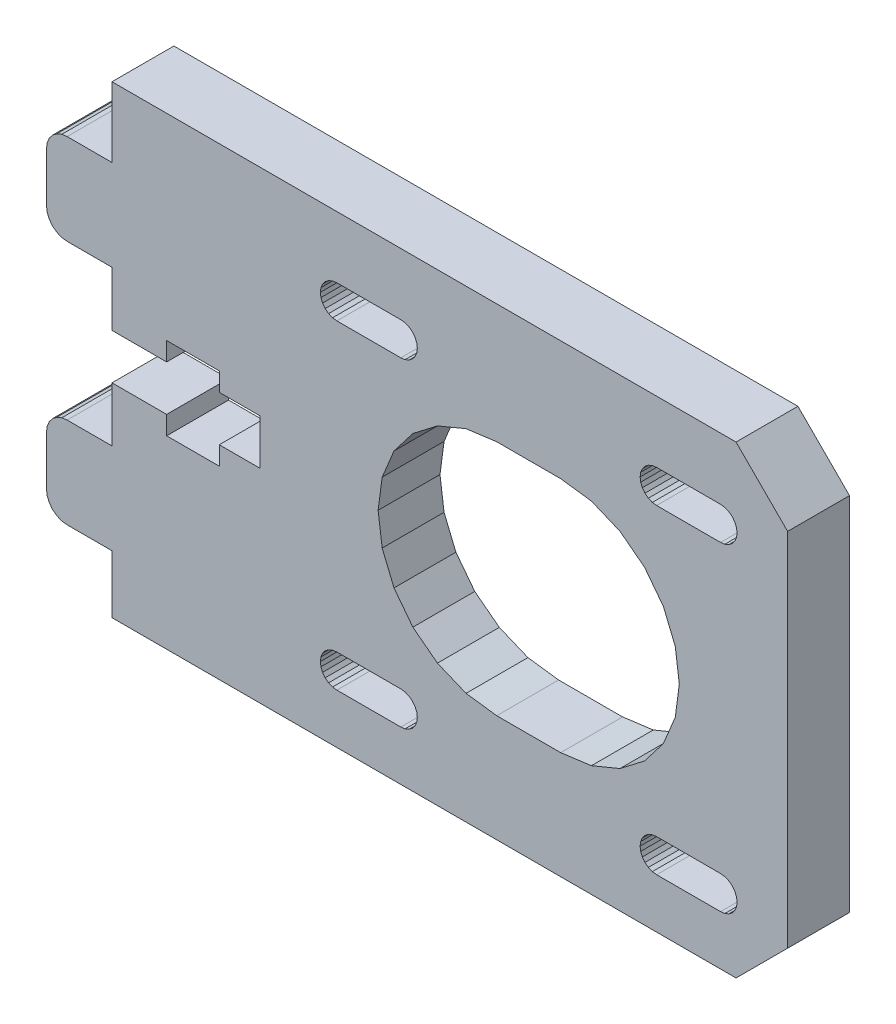
SolidWorks part; units mm, degrees
material "Maple"
ref_plane "Front Plane" through (0, 0, 0) normal (0, 0, 1) x (1, 0, 0)
ref_plane "Top Plane" through (0, 0, 0) normal (0, 1, 0) x (1, 0, 0)
ref_plane "Right Plane" through (0, 0, 0) normal (1, 0, 0) x (0, 0, -1)
sketch "Sketch1" plane through (0, 0, 0) normal (0, 0, 1) x (1, 0, 0)
  line L5378 (-107.063, -155.5566) -> (-112.063, -150.5566)
  line L5379 (-172.563, -150.5566) -> (-112.063, -150.5566)
  line L5380 (-107.063, -155.5566) -> (-107.063, -190.5566)
  line L5381 (-150.763, -156.5357) -> (-151.1771, -156.5902)
  line L5382 (-151.563, -156.7501) -> (-151.8943, -157.0043)
  line L5383 (-152.3085, -158.5498) -> (-152.1486, -158.9357)
  line L5384 (-151.8943, -159.2671) -> (-151.563, -159.5213)
  line L5385 (-151.8943, -157.0043) -> (-152.1486, -157.3357)
  line L5386 (-151.1771, -156.5902) -> (-151.563, -156.7501)
  line L5387 (-152.1486, -158.9357) -> (-151.8943, -159.2671)
  line L5388 (-144.563, -159.7357) -> (-144.1489, -159.6812)
  line L5389 (-150.763, -159.7357) -> (-144.563, -159.7357)
  line L5390 (-151.1771, -159.6812) -> (-150.763, -159.7357)
  line L5391 (-151.563, -159.5213) -> (-151.1771, -159.6812)
  line L5392 (-152.363, -158.1357) -> (-152.3085, -158.5498)
  line L5393 (-152.3085, -157.7216) -> (-152.363, -158.1357)
  line L5394 (-152.1486, -157.3357) -> (-152.3085, -157.7216)
  line L5395 (-150.763, -156.5357) -> (-144.563, -156.5357)
  line L5396 (-144.1489, -156.5902) -> (-144.563, -156.5357)
  line L5397 (-143.763, -156.7501) -> (-144.1489, -156.5902)
  line L5398 (-143.4316, -157.0043) -> (-143.763, -156.7501)
  line L5399 (-143.1773, -157.3357) -> (-143.4316, -157.0043)
  line L5400 (-143.0175, -157.7216) -> (-143.1773, -157.3357)
  line L5401 (-142.963, -158.1357) -> (-143.0175, -157.7216)
  line L5402 (-143.0175, -158.5498) -> (-142.963, -158.1357)
  line L5403 (-143.1773, -158.9357) -> (-143.0175, -158.5498)
  line L5404 (-143.4316, -159.2671) -> (-143.1773, -158.9357)
  line L5405 (-143.763, -159.5213) -> (-143.4316, -159.2671)
  line L5406 (-144.1489, -159.6812) -> (-143.763, -159.5213)
  line L5407 (-172.563, -195.5566) -> (-112.063, -195.5566)
  line L5408 (-143.4316, -188.0043) -> (-143.763, -187.75)
  line L5409 (-151.1771, -187.5902) -> (-151.563, -187.75)
  line L5410 (-152.1486, -188.3357) -> (-152.3085, -188.7216)
  line L5411 (-151.563, -190.5213) -> (-151.1771, -190.6812)
  line L5412 (-152.363, -189.1357) -> (-152.3085, -189.5498)
  line L5413 (-143.763, -190.5213) -> (-143.4316, -190.2671)
  line L5414 (-151.563, -187.75) -> (-151.8943, -188.0043)
  line L5415 (-152.1486, -189.9357) -> (-151.8943, -190.2671)
  line L5416 (-143.0175, -189.5498) -> (-142.963, -189.1357)
  line L5417 (-151.8943, -188.0043) -> (-152.1486, -188.3357)
  line L5418 (-143.1773, -189.9357) -> (-143.0175, -189.5498)
  line L5419 (-151.8943, -190.2671) -> (-151.563, -190.5213)
  line L5420 (-112.063, -195.5566) -> (-107.063, -190.5566)
  line L5421 (-176.913, -189.9357) -> (-177.4306, -189.8675)
  line L5422 (-178.645, -158.3357) -> (-178.8448, -158.8181)
  line L5423 (-177.913, -181.4036) -> (-178.3272, -181.7215)
  line L5424 (-167.263, -177.6357) -> (-167.263, -175.8357)
  line L5425 (-177.913, -157.6036) -> (-178.3272, -157.9215)
  line L5426 (-178.3272, -189.3499) -> (-178.645, -188.9357)
  line L5427 (-158.213, -175.8357) -> (-162.163, -175.8357)
  line L5428 (-158.213, -171.4357) -> (-158.213, -175.8357)
  line L5429 (-178.913, -159.3357) -> (-178.913, -164.1357)
  line L5430 (-178.8448, -158.8181) -> (-178.913, -159.3357)
  line L5431 (-178.3272, -165.5499) -> (-178.645, -165.1357)
  line L5432 (-176.913, -189.9357) -> (-172.563, -189.9357)
  line L5433 (-176.913, -166.1357) -> (-177.4306, -166.0675)
  line L5434 (-178.3272, -157.9215) -> (-178.645, -158.3357)
  line L5435 (-172.563, -157.3357) -> (-176.913, -157.3357)
  line L5436 (-172.563, -181.1357) -> (-176.913, -181.1357)
  line L5437 (-177.4306, -166.0675) -> (-177.913, -165.8677)
  line L5438 (-162.163, -175.8357) -> (-162.163, -177.6357)
  line L5439 (-178.913, -183.1357) -> (-178.913, -187.9357)
  line L5440 (-178.3272, -181.7215) -> (-178.645, -182.1357)
  line L5441 (-178.8448, -188.4533) -> (-178.913, -187.9357)
  line L5442 (-177.4306, -181.2038) -> (-177.913, -181.4036)
  line L5443 (-167.263, -169.6357) -> (-162.163, -169.6357)
  line L5444 (-178.645, -165.1357) -> (-178.8448, -164.6533)
  line L5445 (-177.913, -189.6677) -> (-178.3272, -189.3499)
  line L5446 (-162.163, -169.6357) -> (-162.163, -171.4357)
  line L5447 (-177.913, -165.8677) -> (-178.3272, -165.5499)
  line L5448 (-176.913, -181.1357) -> (-177.4306, -181.2038)
  line L5449 (-178.645, -188.9357) -> (-178.8448, -188.4533)
  line L5450 (-172.563, -171.4357) -> (-167.263, -171.4357)
  line L5451 (-176.913, -166.1357) -> (-172.563, -166.1357)
  line L5452 (-178.645, -182.1357) -> (-178.8448, -182.6181)
  line L5453 (-162.163, -177.6357) -> (-167.263, -177.6357)
  line L5454 (-162.163, -171.4357) -> (-158.213, -171.4357)
  line L5455 (-176.913, -157.3357) -> (-177.4306, -157.4038)
  line L5456 (-178.8448, -182.6181) -> (-178.913, -183.1357)
  line L5457 (-177.4306, -189.8675) -> (-177.913, -189.6677)
  line L5458 (-167.263, -175.8357) -> (-172.563, -175.8357)
  line L5459 (-177.4306, -157.4038) -> (-177.913, -157.6036)
  line L5460 (-178.8448, -164.6533) -> (-178.913, -164.1357)
  line L5461 (-167.263, -171.4357) -> (-167.263, -169.6357)
  line L5462 (-172.563, -171.4357) -> (-172.563, -166.1357)
  line L5463 (-172.563, -181.1357) -> (-172.563, -175.8357)
  line L5464 (-172.563, -157.3357) -> (-172.563, -150.5566)
  line L5465 (-121.363, -189.1357) -> (-121.3085, -189.5498)
  line L5466 (-119.763, -156.5357) -> (-113.563, -156.5357)
  line L5467 (-126.0866, -184.7438) -> (-123.313, -183.595)
  line L5468 (-111.963, -189.1357) -> (-112.0175, -188.7216)
  line L5469 (-146.3711, -176.6121) -> (-145.2223, -179.3857)
  line L5470 (-112.1773, -157.3357) -> (-112.4316, -157.0043)
  line L5471 (-113.563, -190.7357) -> (-113.1489, -190.6812)
  line L5472 (-113.1489, -159.6812) -> (-112.763, -159.5213)
  line L5473 (-141.013, -163.6764) -> (-143.3947, -165.504)
  line L5474 (-120.8944, -190.2671) -> (-120.563, -190.5213)
  line L5475 (-121.3085, -157.7216) -> (-121.363, -158.1357)
  line L5476 (-112.4316, -159.2671) -> (-112.1773, -158.9357)
  line L5477 (-120.8944, -188.0043) -> (-121.1486, -188.3357)
  line L5478 (-119.763, -159.7357) -> (-113.563, -159.7357)
  line L5479 (-112.763, -187.75) -> (-113.1489, -187.5902)
  line L5480 (-119.1037, -179.3857) -> (-117.9548, -176.6121)
  line L5481 (-117.563, -173.6357) -> (-117.9548, -170.6593)
  line L5482 (-135.263, -162.1357) -> (-129.063, -162.1357)
  line L5483 (-112.0175, -158.5498) -> (-111.963, -158.1357)
  line L5484 (-143.4316, -190.2671) -> (-143.1773, -189.9357)
  line L5485 (-150.763, -187.5357) -> (-144.563, -187.5357)
  line L5486 (-121.1486, -189.9357) -> (-120.8944, -190.2671)
  line L5487 (-119.763, -187.5357) -> (-113.563, -187.5357)
  line L5488 (-120.563, -156.7501) -> (-120.8944, -157.0043)
  line L5489 (-112.763, -159.5213) -> (-112.4316, -159.2671)
  line L5490 (-112.763, -156.7501) -> (-113.1489, -156.5902)
  line L5491 (-143.3947, -181.7674) -> (-141.013, -183.595)
  line L5492 (-138.2394, -184.7438) -> (-135.263, -185.1357)
  line L5493 (-113.1489, -156.5902) -> (-113.563, -156.5357)
  line L5494 (-119.763, -156.5357) -> (-120.1771, -156.5902)
  line L5495 (-126.0866, -162.5275) -> (-129.063, -162.1357)
  line L5496 (-112.1773, -188.3357) -> (-112.4316, -188.0043)
  line L5497 (-120.8944, -159.2671) -> (-120.563, -159.5213)
  line L5498 (-113.563, -159.7357) -> (-113.1489, -159.6812)
  line L5499 (-145.2223, -167.8857) -> (-146.3711, -170.6593)
  line L5500 (-146.763, -173.6357) -> (-146.3711, -176.6121)
  line L5501 (-135.263, -162.1357) -> (-138.2394, -162.5275)
  line L5502 (-143.763, -187.75) -> (-144.1489, -187.5902)
  line L5503 (-144.1489, -187.5902) -> (-144.563, -187.5357)
  line L5504 (-120.8944, -157.0043) -> (-121.1486, -157.3357)
  line L5505 (-152.3085, -188.7216) -> (-152.363, -189.1357)
  line L5506 (-143.3947, -165.504) -> (-145.2223, -167.8857)
  line L5507 (-121.3085, -189.5498) -> (-121.1486, -189.9357)
  line L5508 (-145.2223, -179.3857) -> (-143.3947, -181.7674)
  line L5509 (-120.1771, -190.6812) -> (-119.763, -190.7357)
  line L5510 (-152.3085, -189.5498) -> (-152.1486, -189.9357)
  line L5511 (-120.9313, -165.504) -> (-123.313, -163.6764)
  line L5512 (-112.1773, -158.9357) -> (-112.0175, -158.5498)
  line L5513 (-143.0175, -188.7216) -> (-143.1773, -188.3357)
  line L5514 (-119.1037, -167.8857) -> (-120.9313, -165.504)
  line L5515 (-112.0175, -189.5498) -> (-111.963, -189.1357)
  line L5516 (-112.4316, -188.0043) -> (-112.763, -187.75)
  line L5517 (-121.363, -158.1357) -> (-121.3085, -158.5498)
  line L5518 (-150.763, -190.7357) -> (-144.563, -190.7357)
  line L5519 (-112.763, -190.5213) -> (-112.4316, -190.2671)
  line L5520 (-144.563, -190.7357) -> (-144.1489, -190.6812)
  line L5521 (-141.013, -183.595) -> (-138.2394, -184.7438)
  line L5522 (-120.1771, -159.6812) -> (-119.763, -159.7357)
  line L5523 (-119.763, -190.7357) -> (-113.563, -190.7357)
  line L5524 (-135.263, -185.1357) -> (-129.063, -185.1357)
  line L5525 (-120.1771, -187.5902) -> (-120.563, -187.75)
  line L5526 (-112.4316, -157.0043) -> (-112.763, -156.7501)
  line L5527 (-151.1771, -190.6812) -> (-150.763, -190.7357)
  line L5528 (-142.963, -189.1357) -> (-143.0175, -188.7216)
  line L5529 (-121.1486, -158.9357) -> (-120.8944, -159.2671)
  line L5530 (-120.9313, -181.7674) -> (-119.1037, -179.3857)
  line L5531 (-143.1773, -188.3357) -> (-143.4316, -188.0043)
  line L5532 (-121.1486, -157.3357) -> (-121.3085, -157.7216)
  line L5533 (-138.2394, -162.5275) -> (-141.013, -163.6764)
  line L5534 (-113.1489, -187.5902) -> (-113.563, -187.5357)
  line L5535 (-121.3085, -158.5498) -> (-121.1486, -158.9357)
  line L5536 (-112.0175, -188.7216) -> (-112.1773, -188.3357)
  line L5537 (-112.1773, -189.9357) -> (-112.0175, -189.5498)
  line L5538 (-120.563, -159.5213) -> (-120.1771, -159.6812)
  line L5539 (-150.763, -187.5357) -> (-151.1771, -187.5902)
  line L5540 (-112.0175, -157.7216) -> (-112.1773, -157.3357)
  line L5541 (-120.563, -187.75) -> (-120.8944, -188.0043)
  line L5542 (-119.763, -187.5357) -> (-120.1771, -187.5902)
  line L5543 (-121.3085, -188.7216) -> (-121.363, -189.1357)
  line L5544 (-121.1486, -188.3357) -> (-121.3085, -188.7216)
  line L5545 (-129.063, -185.1357) -> (-126.0866, -184.7438)
  line L5546 (-144.1489, -190.6812) -> (-143.763, -190.5213)
  line L5547 (-113.1489, -190.6812) -> (-112.763, -190.5213)
  line L5548 (-120.563, -190.5213) -> (-120.1771, -190.6812)
  line L5549 (-120.1771, -156.5902) -> (-120.563, -156.7501)
  line L5550 (-123.313, -163.6764) -> (-126.0866, -162.5275)
  line L5551 (-123.313, -183.595) -> (-120.9313, -181.7674)
  line L5552 (-117.9548, -176.6121) -> (-117.563, -173.6357)
  line L5553 (-111.963, -158.1357) -> (-112.0175, -157.7216)
  line L5554 (-112.4316, -190.2671) -> (-112.1773, -189.9357)
  line L5555 (-117.9548, -170.6593) -> (-119.1037, -167.8857)
  line L5556 (-146.3711, -170.6593) -> (-146.763, -173.6357)
  line L8417 (-172.563, -195.5566) -> (-172.563, -189.9357)
  line L9307 (-149.19, -184.6426) -> (-151.3504, -182.576)
  line L9308 (-151.3504, -182.576) -> (-151.3504, -184.6426)
  line L9309 (-151.3504, -184.6426) -> (-151.3504, -180.3347)
  line L9310 (-151.3504, -180.3347) -> (-151.3504, -182.576)
  line L9311 (-151.3504, -182.576) -> (-149.19, -180.3347)
  line L9312 (-149.19, -180.3347) -> (-151.3504, -182.576)
  line L9313 (-151.3504, -182.576) -> (-149.19, -184.6426)
  line L9314 (-151.3504, -182.576) -> (-149.19, -180.3347)
  line L9315 (-151.3504, -184.6426) -> (-151.3504, -182.576)
  line L9316 (-149.19, -184.6426) -> (-151.3504, -182.576)
  line L9317 (-151.3504, -182.576) -> (-151.3504, -180.3347)
extrude "Boss-Extrude1" add sketch "Sketch1" along normal blind 6
